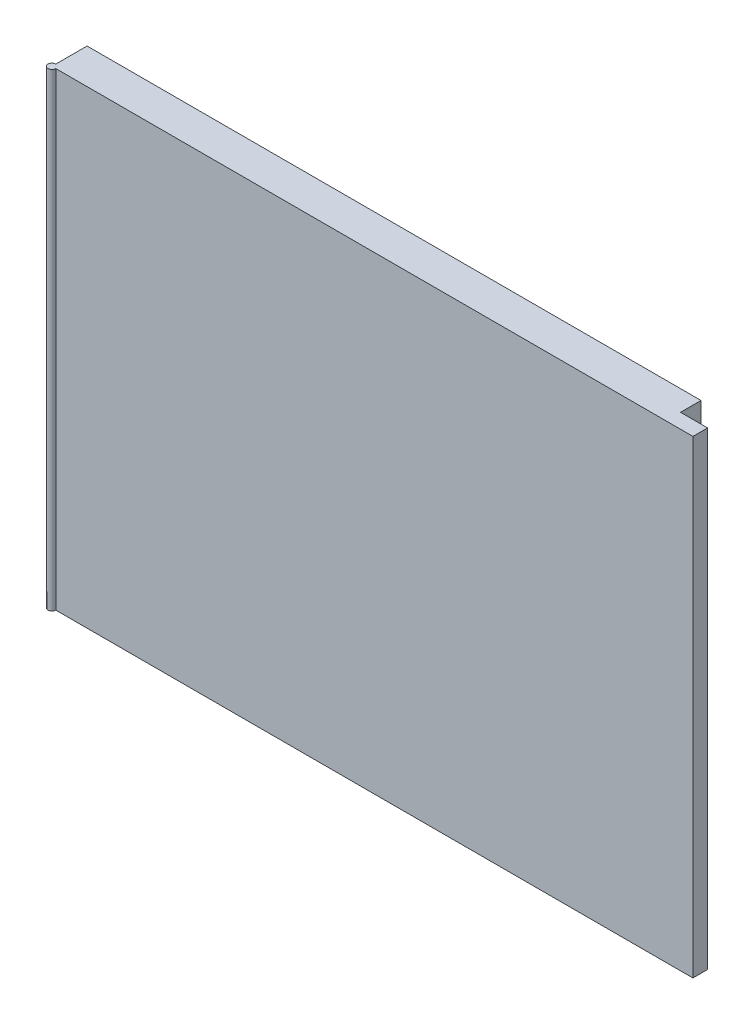
SolidWorks part; units mm, degrees
ref_plane "Спереди" through (0, 0, 0) normal (0, 0, 1) x (1, 0, 0)
ref_plane "Сверху" through (0, 0, 0) normal (0, 1, 0) x (1, 0, 0)
ref_plane "Справа" through (0, 0, 0) normal (1, 0, 0) x (0, 0, -1)
sketch "Эскиз1" plane through (0, 0, 0) normal (0, 1, 0) x (1, 0, 0)
  line L0 (5, 0) -> (820, 0)
  line L1 (0, 5) -> (0, 45)
  line L2 (0, 45) -> (785.3632, 45)
  line L3 (785.3632, 45) -> (785.3632, 18.8004)
  line L4 (785.3632, 18.8004) -> (820, 18.8004)
  line L5 (820, 18.8004) -> (820, 0)
  arc A0 (0, 5) -> (5, 0) centre (0, 0) ccw
extrude "Бобышка-Вытянуть1" add sketch "Эскиз1" along normal blind 600
